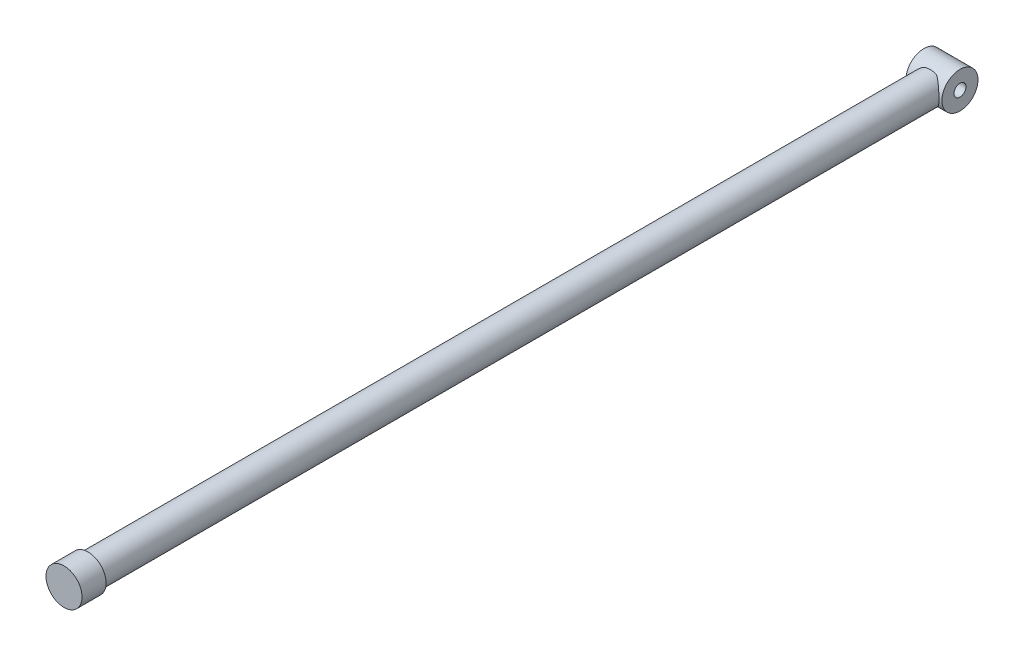
SolidWorks part; units mm, degrees
ref_plane "Ön Düzlem" through (0, 0, 0) normal (0, 0, 1) x (1, 0, 0)
ref_plane "Üst Düzlem" through (0, 0, 0) normal (0, 1, 0) x (1, 0, 0)
ref_plane "Sağ Düzlem" through (0, 0, 0) normal (1, 0, 0) x (0, 0, -1)
sketch "Çizim1" plane through (0, 0, 0) normal (0, 0, 1) x (1, 0, 0)
  circle A0 centre (0, 0) radius 1.5
  dimension "D1" = 3
extrude "Yükseklik-Ekstrüzyon1" add sketch "Çizim1" along normal mid plane 2
sketch "Çizim2" plane through (0, 0, -1) normal (0, 0, -1) x (-1, 0, 0)
  circle A0 centre (0, 0) radius 1.25
  dimension "D1" = 2.5
extrude "Yükseklik-Ekstrüzyon2" add sketch "Çizim2" along normal blind 70
ref_plane "Düzlem1" through (1.25, 0, 0) normal (1, 0, 0) x (0, 0, -1)
sketch "Çizim5" plane through (0, 0, 0) normal (1, 0, 0) x (0, 0, -1)
  line L0 (71, 1.25) -> (1, 1.25) construction
  circle A0 centre (72, 0) radius 0.5
  circle A1 centre (72, 0) radius 1.5
  dimension "D1" = 1
  dimension "D2" = 3
  dimension "D4" = 1.25
  dimension "D3" = 72
extrude "Yükseklik-Ekstrüzyon5" add sketch "Çizim5" against normal mid plane 3
